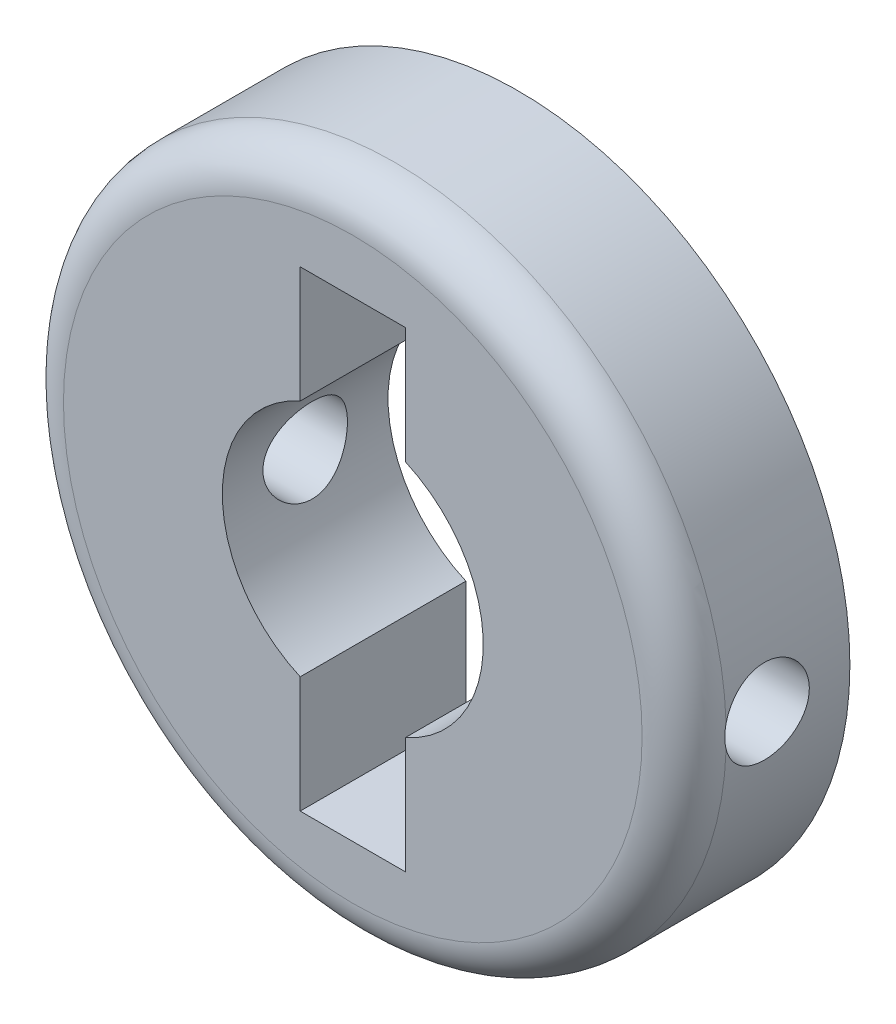
SolidWorks part; units mm, degrees
material "ABS"
ref_plane "Front Plane" through (0, 0, 0) normal (0, 0, 1) x (1, 0, 0)
ref_plane "Top Plane" through (0, 0, 0) normal (0, 1, 0) x (1, 0, 0)
ref_plane "Right Plane" through (0, 0, 0) normal (1, 0, 0) x (0, 0, -1)
sketch "Sketch1" plane through (0, 0, 0) normal (0, 0, 1) x (1, 0, 0)
  line L0 (0, 3.937) -> (0, 7.112) construction
  line L1 (1.5875, 3.6028) -> (1.5875, 7.112)
  line L2 (-1.5875, 3.6028) -> (-1.5875, 7.112)
  line L3 (-1.5875, 3.937) -> (-1.5875, 7.112) construction
  line L4 (1.5875, 7.112) -> (-1.5875, 7.112)
  line L5 (1.5875, 3.937) -> (1.5875, 7.112) construction
  line L6 (0, 0) -> (3.937, 0) construction
  line L7 (0, -3.937) -> (0, -7.112) construction
  line L8 (1.5875, -7.112) -> (-1.5875, -7.112)
  line L9 (-1.5875, -3.6028) -> (-1.5875, -7.112)
  line L10 (1.5875, -3.6028) -> (1.5875, -7.112)
  arc A0 (1.5875, -3.6028) -> (1.5875, 3.6028) centre (0, 0) ccw
  circle A1 centre (0, 0) radius 10
  arc A2 (-1.5875, 3.6028) -> (-1.5875, -3.6028) centre (0, 0) ccw
  circle A3 centre (0, 0) radius 3.937 construction
  dimension "D1" = 7.874
  dimension "D2" = 20
  dimension "D5" = 3.175
  dimension "D3" = 1.5875
  dimension "D4" = 1.5875
extrude "Boss-Extrude1" add sketch "Sketch1" along normal mid plane 5
sketch "Sketch4" plane through (0, 0, 0) normal (1, 0, 0) x (0, 0, -1)
  circle A0 centre (0, 0) radius 1.275
  dimension "D1" = 2.55
extrude "Cut-Extrude1" cut sketch "Sketch4" against normal through all both and the other way through all
fillet "Fillet1" radius 1.27 1 edges at (10, 0, 2.5)
